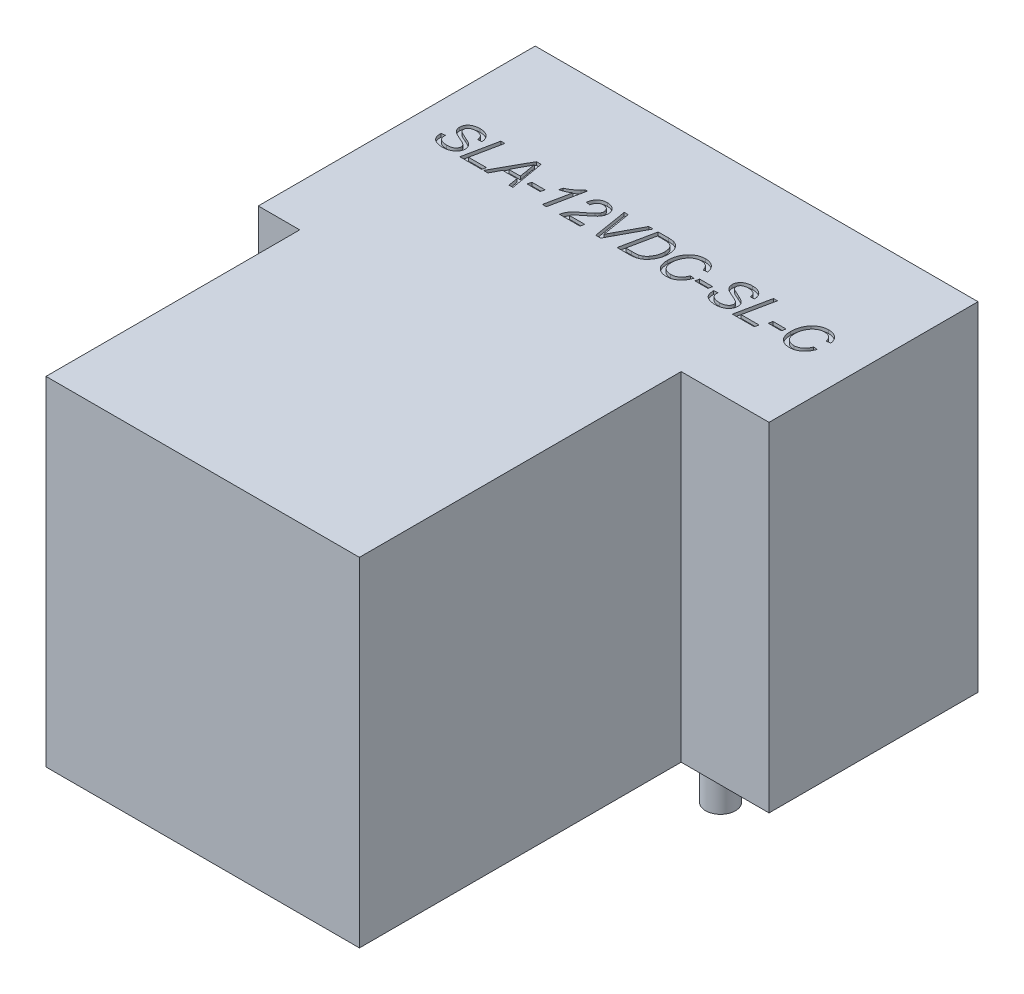
SolidWorks part; units mm, degrees
ref_plane "Спереди" through (0, 0, 0) normal (0, 0, 1) x (1, 0, 0)
ref_plane "Сверху" through (0, 0, 0) normal (0, 1, 0) x (1, 0, 0)
ref_plane "Справа" through (0, 0, 0) normal (1, 0, 0) x (0, 0, -1)
sketch "Эскиз1" plane through (0, 0, 0) normal (0, 1, 0) x (1, 0, 0)
  line L0 (-12.5746, 16.9126) -> (14.1254, 16.9126)
  line L1 (14.1254, 16.9126) -> (14.1254, 4.3126)
  line L2 (14.1254, 4.3126) -> (8.8254, 4.3126)
  line L3 (8.8254, 4.3126) -> (8.8254, -15.0874)
  line L4 (8.8254, -15.0874) -> (-10.0746, -15.0874)
  line L5 (-10.0746, -15.0874) -> (-10.0746, 0.2126)
  line L6 (-10.0746, 0.2126) -> (-12.5746, 0.2126)
  line L7 (-12.5746, 16.9126) -> (-12.5746, 0.2126)
  line L8 (-15.6445, 0) -> (11.7592, 0) construction
  line L9 (0, 19.977) -> (0, -19.6057) construction
  dimension "D1" = 26.7
  dimension "D2" = 32
  dimension "D3" = 12.6
  dimension "D4" = 16.7
  dimension "D5" = 5.3
  dimension "D6" = 2.5
extrude "Бобышка-Вытянуть1" add sketch "Эскиз1" along normal blind 20.4
sketch "Эскиз2" plane through (0, 0, 0) normal (0, -1, 0) x (1, 0, 0)
  line L0 (-10.0746, 15.0874) -> (8.8254, 15.0874) construction
  circle A0 centre (-5.1, 8.5874) radius 0.4
  circle A1 centre (5.1, 8.5874) radius 0.4
  circle A2 centre (-8.9, -4.1126) radius 0.9
  circle A3 centre (8.9, -6.6126) radius 0.9
  circle A4 centre (8.9, -14.2126) radius 0.9
  point P13 (0, 0)
  dimension "D1" = 0.8
  dimension "D2" = 0.8
  dimension "D6" = 1.8
  dimension "D7" = 1.8
  dimension "D8" = 1.8
  dimension "D3" = 10.2
  dimension "D4" = 6.5
  dimension "D5" = 5.1
  dimension "D9" = 7.6
  dimension "D10" = 8.9
  dimension "D11" = 15.2
  dimension "D12" = 2.5
  dimension "D13" = 3.8
  dimension "D14" = 17.8
extrude "Бобышка-Вытянуть2" add sketch "Эскиз2" along normal blind 3.2
sketch "Эскиз3" plane through (0, 20.4, 0) normal (0, 1, 0) x (1, 0, 0)
  text T0 "SLA-12VDC-SL-C" font "Arial" height in points 8
extrude "Вырез-Вытянуть1" cut sketch "Эскиз3" against normal blind 0.2
